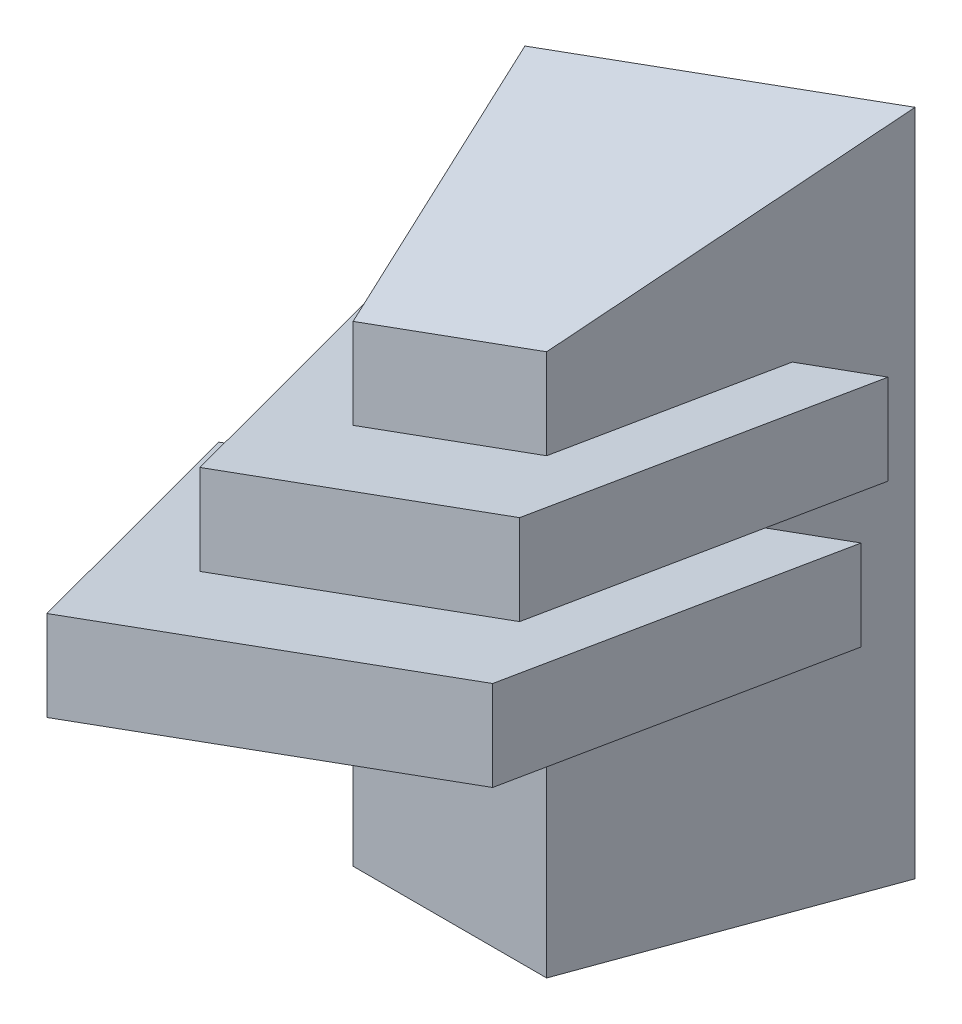
SolidWorks part; units mm, degrees
other "Perspective"
ref_plane "Front" through (0, 0, 0) normal (0, 0, 1) x (1, 0, 0)
ref_plane "Top" through (0, 0, 0) normal (0, 1, 0) x (1, 0, 0)
ref_plane "Right" through (0, 0, 0) normal (1, 0, 0) x (0, 0, -1)
sketch "Sketch1" plane through (0, 0, 0) normal (0, 1, 0) x (1, 0, 0)
  line L0 (21.0063, 30) -> (53.2489, 30)
  line L1 (53.2489, 30) -> (69.6276, 75)
  line L2 (69.6276, 75) -> (4.6276, 75)
  line L3 (4.6276, 75) -> (21.0063, 30)
  line L4 (4.6276, 75) -> (4.6276, 30) construction
extrude "Extrude1" add sketch "Sketch1" along normal blind 111.3037
sketch "Sketch2" plane through (0, 0, -30) normal (0, 0, 1) x (1, 0, 0)
  line L0 (69.6276, 111.3037) -> (4.6276, 111.3037)
  line L1 (4.6276, 111.3037) -> (4.6276, 87.6456)
  line L2 (4.6276, 111.3037) -> (4.6276, 0) construction
  line L3 (4.6276, 87.6456) -> (69.6276, 111.3037)
  dimension "D1" = 20
extrude "Cut-Extrude1" cut sketch "Sketch2" against normal through all
sketch "Sketch3" plane through (0, 0, -30) normal (0, 0, 1) x (1, 0, 0)
  line L0 (69.6276, 96.3037) -> (4.6276, 72.6456)
  line L1 (69.6276, 111.3037) -> (69.6276, 0) construction
  line L2 (4.6276, 87.6456) -> (4.6276, 0) construction
  line L3 (21.0063, 93.607) -> (53.2489, 105.3424) construction
  line L4 (4.6276, 57.6456) -> (69.6276, 81.3037)
  line L5 (4.6276, 42.6456) -> (69.6276, 66.3037)
  line L6 (4.6276, 27.6456) -> (69.6276, 51.3037)
  dimension "D1" = 15
  dimension "D2" = 15
  dimension "D3" = 15
  dimension "D4" = 15
ref_plane "Plane1" through (-17.8421, 49.0206, 16.3402) normal (0.3264, -0.8967, -0.2989) x (0.9452, 0.3096, 0.1032)
sketch "Sketch4" plane through (-17.8421, 49.0206, 16.3402) normal (0.3264, -0.8967, -0.2989) x (0.9452, 0.3096, 0.1032)
  line L1 (102.6415, -52.9743) -> (8.9368, -52.9743)
  line L2 (102.6415, -52.9743) -> (102.6415, -109.7585)
  line L3 (102.6415, -109.7585) -> (8.9368, -109.7585)
  line L4 (8.9368, -52.9743) -> (8.9368, -109.7585)
extrude "Cut-Extrude2" cut sketch "Sketch4" against normal blind 111.3037
ref_plane "Plane2" through (0.5413, -1.4873, 0) normal (-0.342, 0.9397, 0) x (-0.9397, -0.342, 0)
ref_plane "Plane3" through (-8.3438, 22.9244, 0) normal (-0.342, 0.9397, 0) x (-0.9397, -0.342, 0)
sketch "Sketch6" plane through (0, 0, 0) normal (0, 1, 0) x (1, 0, 0)
  line L0 (-16.3787, 45) -> (90.6338, 45)
  line L1 (90.6338, 45) -> (74.2551, 0)
  line L2 (74.2551, 0) -> (0, 0)
  line L3 (0, 0) -> (-16.3787, 45)
  line L4 (4.6276, 75) -> (21.0063, 30) construction
  line L5 (53.2489, 30) -> (69.6276, 75) construction
  line L10 (21.0063, 30) -> (53.2489, 30) construction
  dimension "D1" = 15
  dimension "D2" = 30
ref_plane "Plane4" through (-13.1647, 36.1698, 0) normal (-0.342, 0.9397, 0) x (-0.9397, -0.342, 0)
extrude "Extrude2" add sketch "Sketch6" along normal blind 111.3037 separate body
sketch "Sketch11" plane through (-8.3438, 22.9244, 0) normal (-0.342, 0.9397, 0) x (-0.9397, -0.342, 0)
  line L1 (-127.4113, 3.9923) -> (21.5604, 3.9923)
  line L2 (-127.4113, 3.9923) -> (-127.4113, -52.9605)
  line L3 (-127.4113, -52.9605) -> (21.5604, -52.9605)
  line L4 (21.5604, 3.9923) -> (21.5604, -52.9605)
extrude "Cut-Extrude3" cut sketch "Sketch11" against normal blind 60
sketch "Sketch12" plane through (-13.1647, 36.1698, 0) normal (-0.342, 0.9397, 0) x (-0.9397, -0.342, 0)
  line L1 (-130.7061, 7.2871) -> (18.9717, 7.2871)
  line L2 (-130.7061, 7.2871) -> (-130.7061, -51.0778)
  line L3 (-130.7061, -51.0778) -> (18.9717, -51.0778)
  line L4 (18.9717, 7.2871) -> (18.9717, -51.0778)
extrude "Cut-Extrude4" cut sketch "Sketch12" along normal blind 80
ref_plane "Plane5" through (-17.9856, 49.4151, 0) normal (-0.342, 0.9397, 0) x (-0.9397, -0.342, 0)
sketch "Sketch13" plane through (0, 0, 0) normal (0, 1, 0) x (1, 0, 0)
  line L0 (-5.8756, 60) -> (80.1307, 60)
  line L1 (80.1307, 60) -> (63.752, 15)
  line L2 (63.752, 15) -> (10.5031, 15)
  line L3 (10.5031, 15) -> (-5.8756, 60)
  line L4 (-16.3787, 45) -> (0, 0) construction
  line L5 (74.2551, 0) -> (90.6338, 45) construction
  line L6 (90.6338, 45) -> (-16.3787, 45) construction
  line L7 (21.0063, 30) -> (53.2489, 30) construction
  dimension "D1" = 15
  dimension "D2" = 15
  dimension "D3" = 15
  dimension "D4" = 15
extrude "Extrude3" add sketch "Sketch13" along normal blind 90 separate body
sketch "Sketch14" plane through (-17.9856, 49.4151, 0) normal (-0.342, 0.9397, 0) x (-0.9397, -0.342, 0)
  line L1 (-116.4827, -13.6763) -> (-4.6285, -13.6763)
  line L2 (-116.4827, -13.6763) -> (-116.4827, -67.1439)
  line L3 (-116.4827, -67.1439) -> (-4.6285, -67.1439)
  line L4 (-4.6285, -13.6763) -> (-4.6285, -67.1439)
extrude "Cut-Extrude5" cut sketch "Sketch14" along normal blind 40
sketch "Sketch15" plane through (-13.1647, 36.1698, 0) normal (-0.342, 0.9397, 0) x (-0.9397, -0.342, 0)
  line L1 (-118.8353, -12.3931) -> (8.0171, -12.3931)
  line L2 (-118.8353, -12.3931) -> (-118.8353, -64.7913)
  line L3 (-118.8353, -64.7913) -> (8.0171, -64.7913)
  line L4 (8.0171, -12.3931) -> (8.0171, -64.7913)
extrude "Cut-Extrude6" cut sketch "Sketch15" against normal blind 70
